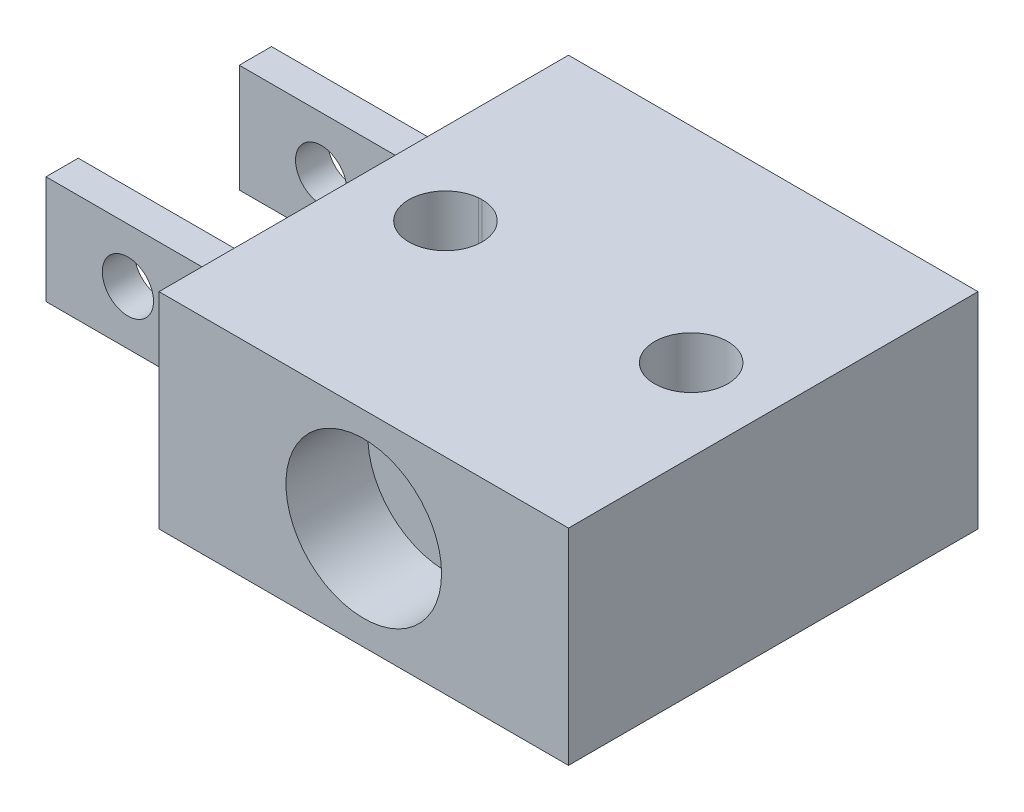
SolidWorks part; units mm, degrees
ref_plane "Front Plane" through (0, 0, 0) normal (0, 0, 1) x (1, 0, 0)
ref_plane "Top Plane" through (0, 0, 0) normal (0, 1, 0) x (1, 0, 0)
ref_plane "Right Plane" through (0, 0, 0) normal (1, 0, 0) x (0, 0, -1)
sketch "Sketch2" plane through (0, 0, 0) normal (0, 1, 0) x (1, 0, 0)
  line L0 (6.3181, -7.986) -> (6.3181, 4.206) construction
  line L1 (-6.3819, 4.46) -> (6.3181, 4.46)
  line L2 (-6.3819, 4.46) -> (-6.3819, -8.24)
  line L3 (-6.3819, -8.24) -> (6.3181, -8.24)
  line L4 (6.3181, 4.46) -> (6.3181, -8.24)
  line L5 (6.0641, -8.24) -> (-6.1279, -8.24) construction
  line L6 (-6.3819, 4.206) -> (-6.3819, -7.986) construction
  line L7 (6.0641, 4.46) -> (-6.1279, 4.46) construction
extrude "Boss-Extrude4" add sketch "Sketch2" along normal blind 3.6068 and the other way blind 2.7686
sketch "Sketch3" plane through (-6.3819, 0, 0) normal (-1, 0, 0) x (0, 0, 1)
  line L1 (-1.5988, 2.0942) -> (-0.5988, 2.0942)
  line L2 (-1.5988, 2.0942) -> (-1.5988, -1.2586)
  line L3 (-1.5988, -1.2586) -> (-0.5988, -1.2586)
  line L4 (-0.5988, 2.0942) -> (-0.5988, -1.2586)
  line L5 (4.3948, 2.0942) -> (5.3948, 2.0942)
  line L6 (4.3948, 2.0942) -> (4.3948, -1.2586)
  line L7 (4.3948, -1.2586) -> (5.3948, -1.2586)
  line L8 (5.3948, 2.0942) -> (5.3948, -1.2586)
extrude "Boss-Extrude5" add sketch "Sketch3" along normal blind 6.35
sketch "Sketch4" plane through (0, 0, 5.3948) normal (0, 0, 1) x (1, 0, 0)
  circle A0 centre (-10.1919, 0.4178) radius 0.7937
extrude "Cut-Extrude1" cut sketch "Sketch4" against normal through all
sketch "Sketch5" plane through (0, 0, 8.24) normal (0, 0, 1) x (1, 0, 0)
  circle A0 centre (-0.0319, 0.4178) radius 2.413
extrude "Cut-Extrude2" cut sketch "Sketch5" against normal blind 2.54
sketch "Sketch7" plane through (0, 3.6068, 0) normal (0, 1, 0) x (1, 0, 0)
  circle A0 centre (-3.8419, -1.8961) radius 1.1364
  circle A1 centre (3.7781, -1.8961) radius 1.1364
  spline S0 degree 3 poles (224.9632, 2990.966) (-6.3937, -27.9554) (-0.1068, -0.1464) (3.999, -0.7798) (4.1068, -0.8066) (4.2461, -0.8565) (4.4102, -0.9441) (4.5825, -1.0856) (4.724, -1.258) (4.8291, -1.4547) (4.8939, -1.6681) (4.9157, -1.89) (4.8939, -2.1119) (4.8291, -2.3253) (4.724, -2.522) (4.5825, -2.6944) (4.4102, -2.8359) (4.2461, -2.9235) (4.1068, -2.9734) (3.999, -3.0002) (-0.1068, -3.6336) (-6.3936, 24.1749) (224.957, -2994.6661) knots -3.412076 -3.412076 -3.412076 -3.412076 0.031278 0.062557 0.093835 0.125114 0.187595 0.250076 0.312557 0.375038 0.437519 0.5 0.562481 0.624962 0.687443 0.749924 0.812405 0.874886 0.906165 0.937443 0.968722 4.412046 4.412046 4.412046 4.412046 only from (3.7781, -0.7597) to (3.7781, -3.0203) construction
  spline S1 degree 3 poles (-225.0269, -2994.746) (6.33, 24.1754) (0.0431, -3.6336) (-4.0627, -3.0002) (-4.1705, -2.9734) (-4.3099, -2.9235) (-4.4739, -2.8359) (-4.6463, -2.6944) (-4.7877, -2.522) (-4.8929, -2.3253) (-4.9576, -2.1119) (-4.9795, -1.89) (-4.9576, -1.6681) (-4.8929, -1.4547) (-4.7877, -1.258) (-4.6463, -1.0856) (-4.4739, -0.9441) (-4.3099, -0.8565) (-4.1705, -0.8066) (-4.0627, -0.7798) (0.043, -0.1464) (6.3299, -27.9549) (-225.0208, 2990.8861) knots -3.412076 -3.412076 -3.412076 -3.412076 0.031278 0.062557 0.093835 0.125114 0.187595 0.250076 0.312557 0.375038 0.437519 0.5 0.562481 0.624962 0.687443 0.749924 0.812405 0.874886 0.906165 0.937443 0.968722 4.412046 4.412046 4.412046 4.412046 only from (-3.8419, -3.0203) to (-3.8419, -0.7597) construction
  spline S2 degree 3 poles (3.7781, -0.7597) (3.8151, -0.7607) (3.8891, -0.7628) (3.999, -0.7798) (4.1068, -0.8066) (4.2461, -0.8565) (4.4102, -0.9441) (4.5825, -1.0856) (4.724, -1.258) (4.8291, -1.4547) (4.8939, -1.6681) (4.9157, -1.89) (4.8939, -2.1119) (4.8291, -2.3253) (4.724, -2.522) (4.5825, -2.6944) (4.4102, -2.8359) (4.2461, -2.9235) (4.1068, -2.9734) (3.999, -3.0002) (3.8891, -3.0172) (3.8151, -3.0192) (3.7781, -3.0203) knots 0 0 0 0 0.031278 0.062557 0.093835 0.125114 0.187595 0.250076 0.312557 0.375038 0.437519 0.5 0.562481 0.624962 0.687443 0.749924 0.812405 0.874886 0.906165 0.937443 0.968722 1 1 1 1
  spline S3 degree 3 poles (-3.8419, -3.0203) (-3.8789, -3.0192) (-3.9528, -3.0172) (-4.0627, -3.0002) (-4.1705, -2.9734) (-4.3099, -2.9235) (-4.4739, -2.8359) (-4.6463, -2.6944) (-4.7877, -2.522) (-4.8929, -2.3253) (-4.9576, -2.1119) (-4.9795, -1.89) (-4.9576, -1.6681) (-4.8929, -1.4547) (-4.7877, -1.258) (-4.6463, -1.0856) (-4.4739, -0.9441) (-4.3099, -0.8565) (-4.1705, -0.8066) (-4.0627, -0.7798) (-3.9528, -0.7628) (-3.8789, -0.7607) (-3.8419, -0.7597) knots 0 0 0 0 0.031278 0.062557 0.093835 0.125114 0.187595 0.250076 0.312557 0.375038 0.437519 0.5 0.562481 0.624962 0.687443 0.749924 0.812405 0.874886 0.906165 0.937443 0.968722 1 1 1 1
extrude "Cut-Extrude4" cut sketch "Sketch7" against normal through all
